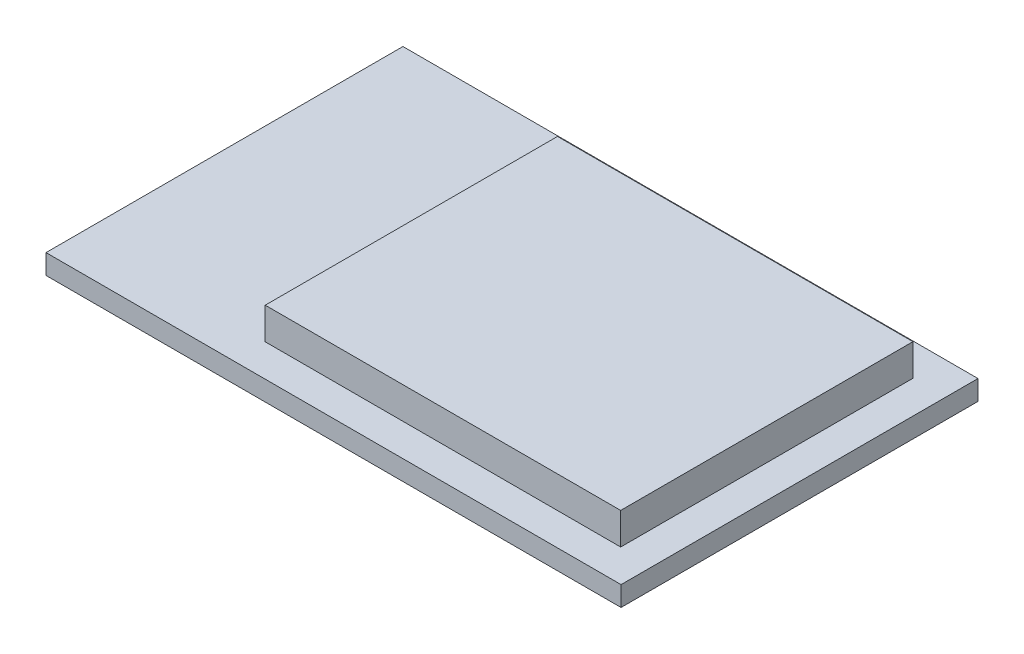
SolidWorks part; units mm, degrees
ref_plane "Front" through (0, 0, 0) normal (0, 0, 1) x (1, 0, 0)
ref_plane "Top" through (0, 0, 0) normal (0, 1, 0) x (1, 0, 0)
ref_plane "Right" through (0, 0, 0) normal (1, 0, 0) x (0, 0, -1)
sketch "Эскиз1" plane through (0, 0, 0) normal (0, 1, 0) x (1, 0, 0)
  line L0 (-14.5, 9) -> (14.5, 9)
  line L1 (-14.5, 9) -> (-14.5, -9)
  line L2 (14.5, 9) -> (14.5, -9)
  line L3 (-14.5, -9) -> (14.5, -9)
  line L4 (-14.5, 9) -> (14.5, -9) construction
  line L5 (14.5, 9) -> (-14.5, -9) construction
  point P1 (0, 0)
extrude "Бобышка-Вытянуть1" add sketch "Эскиз1" along normal blind 1
sketch "Эскиз2" plane through (0, 1, 0) normal (0, 1, 0) x (1, 0, 0)
  line L0 (14.5, -9) -> (14.5, 9) construction
  line L1 (12.85, 0) -> (-5.075, 0) construction
  line L2 (-5.075, -7.3692) -> (12.85, -7.3692)
  line L3 (-5.075, -7.3692) -> (-5.075, 7.3692)
  line L4 (12.85, -7.3692) -> (12.85, 7.3692)
  line L5 (-5.075, 7.3692) -> (12.85, 7.3692)
  line L6 (-5.075, -7.3692) -> (12.85, 7.3692) construction
  line L7 (12.85, -7.3692) -> (-5.075, 7.3692) construction
  circle A0 centre (0, 0) radius 7.375 construction
  circle A1 centre (14.5, 0) radius 1.65 construction
  point P10 (3.8875, 0)
extrude "Бобышка-Вытянуть2" add sketch "Эскиз2" along normal blind 1.6
